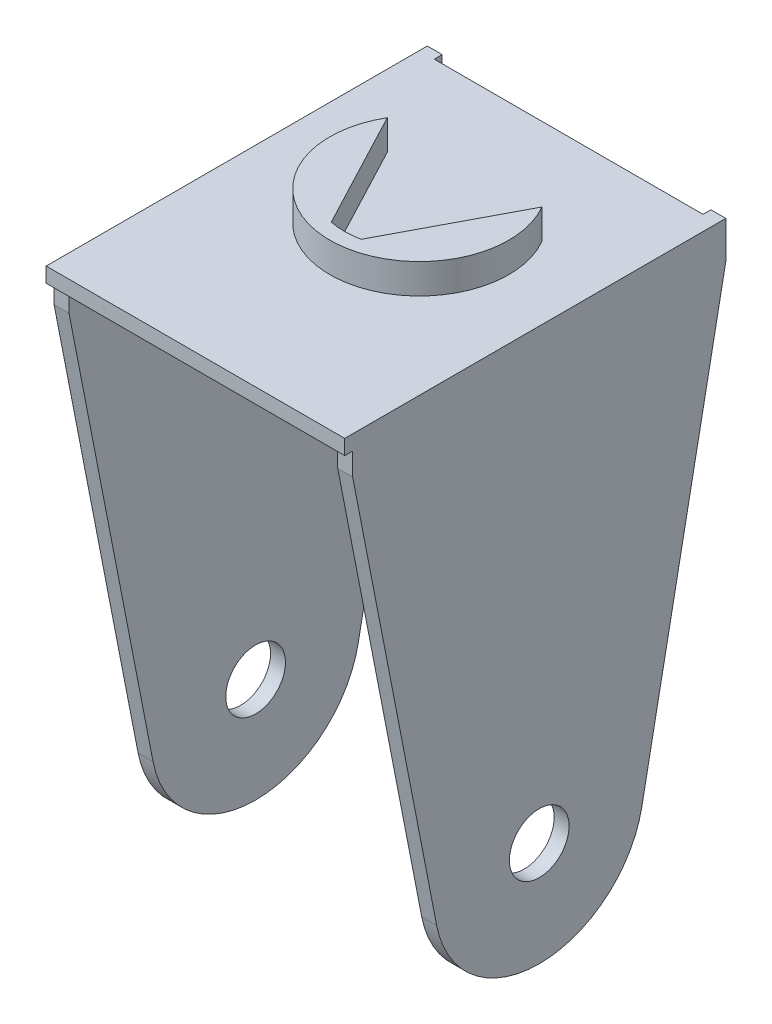
SolidWorks part; units mm, degrees
ref_plane "Front Plane" through (0, 0, 0) normal (0, 0, 1) x (1, 0, 0)
ref_plane "Top Plane" through (0, 0, 0) normal (0, 1, 0) x (1, 0, 0)
ref_plane "Right Plane" through (0, 0, 0) normal (1, 0, 0) x (0, 0, -1)
sketch "Sketch1" plane through (0, 0, 0) normal (1, 0, 0) x (0, 0, -1)
  line L0 (6.7734, -5.4068) -> (-4.4859, 52.2753)
  line L1 (-4.4859, 52.2753) -> (-4.4859, 57.2753)
  line L2 (-4.4859, 57.2753) -> (45.5141, 57.2753)
  line L3 (45.5141, 57.2753) -> (45.5141, 52.2753)
  line L4 (45.5141, 52.2753) -> (34.2548, -5.4068)
  line L5 (20.5141, 98.0411) -> (20.5141, -56.5532) construction
  circle A1 centre (20.5141, -2.7247) radius 14
  point P0 (0, 0)
  point P11 (44.4543, 57.0885)
  dimension "D1" = 28
  dimension "D2" = 60
  dimension "D3" = 5
  dimension "D4" = 50
  dimension "D5" = 5
extrude "Boss-Extrude1" add sketch "Sketch1" against normal blind 2 contours L5 L2 L1 L0 A1 | L2 L5 A1 L4 L3 | A1 L5 | L5 A1
ref_plane "Plane1" through (-20, 0, 0) normal (1, 0, 0) x (0, 0, -1)
ref_plane "Plane2" through (-20, 0, 0) normal (1, 0, 0) x (0, 0, -1)
mirror "Mirror1" about plane through (-20, 0, 0) normal (1, 0, 0) of bodies 101
sketch "Sketch2" plane through (0, 57.2753, 0) normal (0, 1, 0) x (1, 0, 0)
  line L1 (-40, 44.4543) -> (0, 44.4543)
  line L2 (-40, 44.4543) -> (-40, -5.5457)
  line L3 (-40, -5.5457) -> (0, -5.5457)
  line L4 (0, 44.4543) -> (0, -5.5457)
extrude "Boss-Extrude2" add sketch "Sketch2" against normal blind 2
sketch "Sketch3" plane through (0, 57.2753, 0) normal (0, 1, 0) x (1, 0, 0)
  line L0 (0, 19.4543) -> (-40, 19.4543) construction
  line L3 (-40, 19.4543) -> (-20, -5.5457) construction
  line L5 (-20, -5.5457) -> (-20, 45.5141) construction
  line L6 (-2, 45.5141) -> (0, 45.5141) construction
  line L10 (-18, 14.6539) -> (-9.6438, 30.5141)
  line L11 (-22, 14.6539) -> (-30.3562, 30.5141)
  arc A0 (-22, 14.6539) -> (-18, 14.6539) centre (-20, 24.4519) ccw
  arc A1 (-30.3562, 30.5141) -> (-9.6438, 30.5141) centre (-20, 24.4519) ccw
  arc A2 (-22.4, 12.6943) -> (-17.6, 12.6943) centre (-20, 24.4519) ccw construction
  dimension "D3" = 20
  dimension "D1" = 20.7123
  dimension "D2" = 2
  dimension "D4" = 15
extrude "Boss-Extrude3" add sketch "Sketch3" along normal blind 4 contours L11 A1 L10 A0
sketch "Sketch4" plane through (0, 0, 0) normal (1, 0, 0) x (0, 0, -1)
  circle A0 centre (20.5141, -2.7247) radius 4
  arc A1 (6.7734, -5.4068) -> (34.2548, -5.4068) centre (20.5141, -2.7247) ccw construction
  dimension "D1" = 8
extrude "Cut-Extrude1" cut sketch "Sketch4" against normal through all
